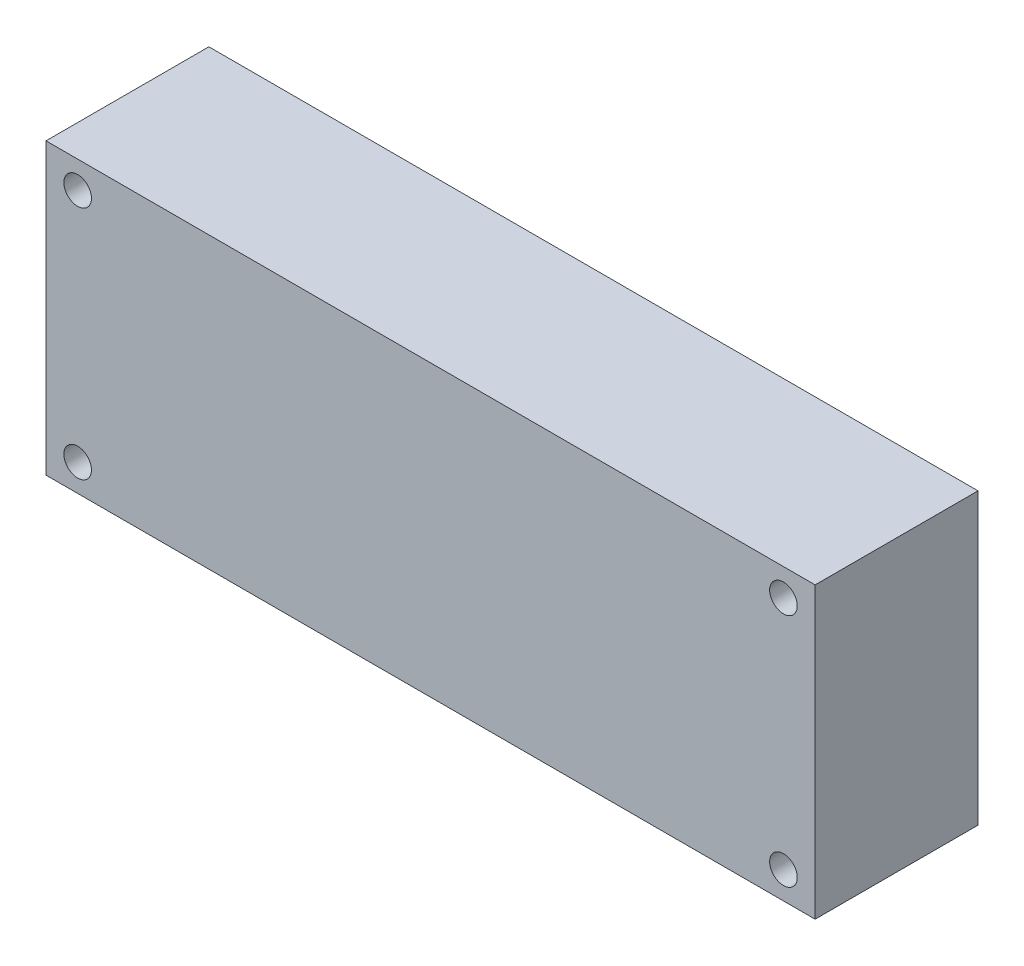
SolidWorks part; units mm, degrees
ref_plane "前视基准面" through (0, 0, 0) normal (0, 0, 1) x (1, 0, 0)
ref_plane "上视基准面" through (0, 0, 0) normal (0, 1, 0) x (1, 0, 0)
ref_plane "右视基准面" through (0, 0, 0) normal (1, 0, 0) x (0, 0, -1)
other "Configuration Table"
sketch "草图1" plane through (0, 0, 0) normal (0, 0, 1) x (1, 0, 0)
  line L1 (-42.5, -16) -> (42.5, -16)
  line L2 (-42.5, -16) -> (-42.5, 16)
  line L3 (-42.5, 16) -> (42.5, 16)
  line L4 (42.5, -16) -> (42.5, 16)
  line L5 (-42.5, -16) -> (42.5, 16) construction
  line L6 (-42.5, 16) -> (42.5, -16) construction
  point P0 (0, 0)
  dimension "D1" = 85
  dimension "D2" = 32
extrude "凸台-拉伸1" add sketch "草图1" along normal blind 18
sketch "草图2" plane through (0, 0, 18) normal (0, 0, 1) x (1, 0, 0)
  line L1 (-39, -13) -> (39, -13) construction
  line L2 (-39, -13) -> (-39, 13) construction
  line L3 (-39, 13) -> (39, 13) construction
  line L4 (39, -13) -> (39, 13) construction
  line L5 (-39, -13) -> (39, 13) construction
  line L6 (-39, 13) -> (39, -13) construction
  circle A0 centre (39, 13) radius 1.525
  circle A1 centre (39, -13) radius 1.525
  circle A2 centre (-39, -13) radius 1.525
  circle A3 centre (-39, 13) radius 1.525
  point P0 (0, 0)
  dimension "D3" = 3.05
  dimension "D1" = 26
  dimension "D2" = 78
extrude "切除-拉伸1" cut sketch "草图2" against normal through all both and the other way through all
